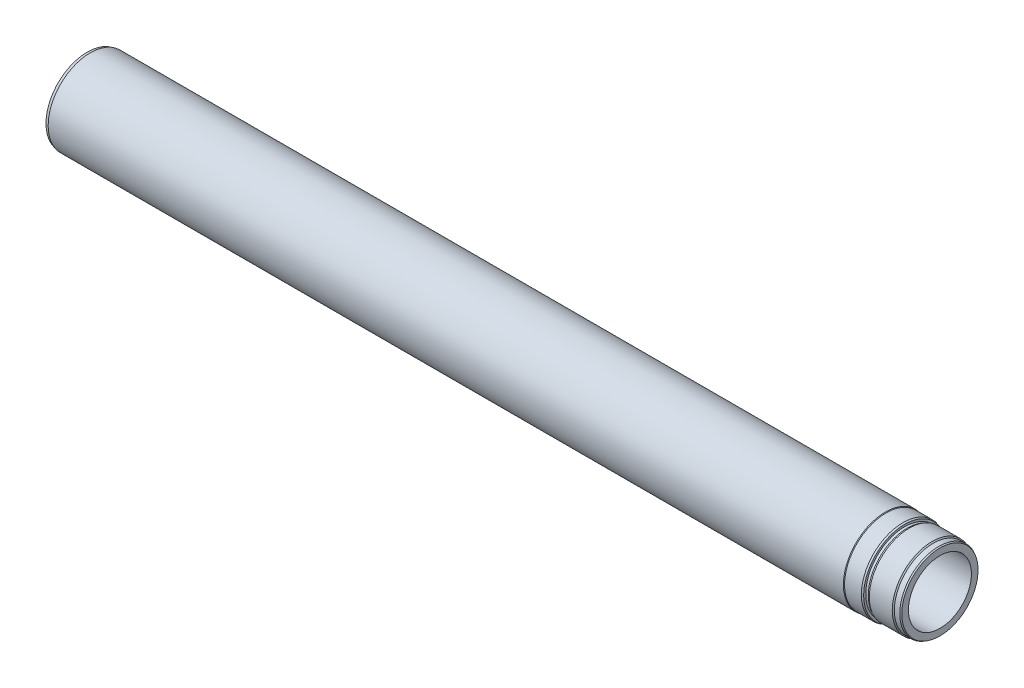
SolidWorks part; units mm, degrees
ref_plane "Front" through (0, 0, 0) normal (0, 0, 1) x (1, 0, 0)
ref_plane "Top" through (0, 0, 0) normal (0, 1, 0) x (1, 0, 0)
ref_plane "Right" through (0, 0, 0) normal (1, 0, 0) x (0, 0, -1)
sketch "Sketch1" plane through (0, 0, 0) normal (0, 0, 1) x (1, 0, 0)
  line L0 (-1014.5, 0) -> (0, 0) construction
  line L1 (0, 37.5) -> (0, 45.384)
  line L2 (-1.5, 46.25) -> (-8, 46.25)
  line L3 (-8, 46.25) -> (-9.25, 47.5)
  line L4 (-64.866, 50) -> (-1011, 50)
  line L5 (-1011, 50) -> (-1014.5, 49.0622)
  line L6 (-1013, 40.25) -> (-992.5, 40.25)
  line L7 (-1014.5, 49.0622) -> (-1014.5, 41.75)
  line L8 (-931.461, 37.5) -> (0, 37.5)
  line L9 (-9.25, 47.5) -> (-36.5467, 47.5)
  line L10 (-42, 48.7721) -> (-42, 46.25)
  line L11 (-44, 49.5) -> (-64, 49.5)
  line L12 (-64, 49.5) -> (-64.866, 50)
  line L13 (-42, 46.25) -> (-39, 46.25)
  line L14 (-39, 46.25) -> (-36.5467, 47.5)
  line L15 (-1.5, 46.25) -> (0, 45.384)
  line L16 (-42, 48.7721) -> (-44, 49.5)
  line L17 (-1014.5, 41.75) -> (-1013, 40.25)
  line L19 (-992.5, 40.25) -> (-990.192, 38.9175)
  line L20 (-990.192, 38.9175) -> (-939.5, 38.9175)
  line L21 (-939.5, 38.9175) -> (-931.461, 37.5)
  dimension "D22" = 15
  dimension "D24" = 1.5
  dimension "D4" = 95
  dimension "D5" = 75
  dimension "D6" = 3.5
  dimension "D7" = 8
  dimension "D8" = 92.5
  dimension "D9" = 45
  dimension "D10" = 27
  dimension "D11" = 99
  dimension "D12" = 3
  dimension "D13" = 100
  dimension "D14" = 1014.5
  dimension "D15" = 30
  dimension "D16" = 64
  dimension "D17" = 42
  dimension "D18" = 1.5
  dimension "D19" = 30
  dimension "D20" = 2
  dimension "D21" = 20
  dimension "D23" = 80.5
  dimension "D25" = 22
  dimension "D26" = 30
  dimension "D27" = 77.835
  dimension "D29" = 10
  dimension "D30" = 75
  dimension "D31" = 45
  dimension "D32" = 92.5
revolve "Base-Revolve" add sketch "Sketch1" angle 360 about L0
cosmetic thread "Cosmetic Thread1" parameters "D1"=42, "D2"=80
cosmetic thread "Cosmetic Thread2" parameters "D2"=92.835
